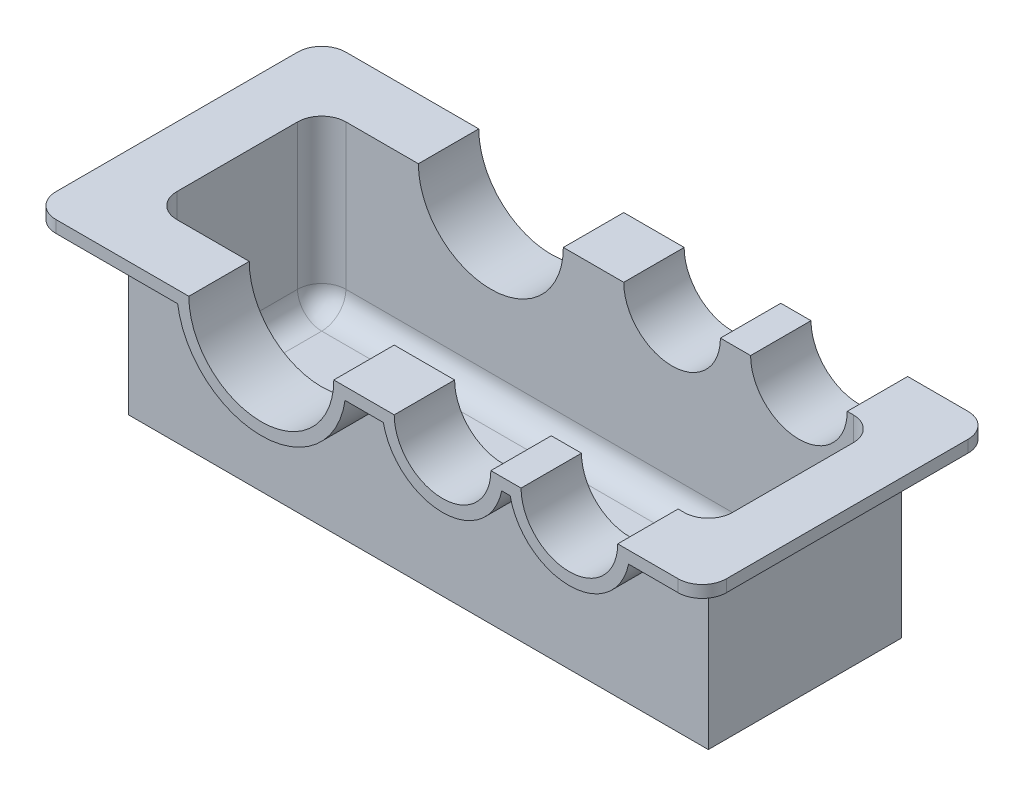
SolidWorks part; units mm, degrees
ref_plane "Front Plane" through (0, 0, 0) normal (0, 0, 1) x (1, 0, 0)
ref_plane "Top Plane" through (0, 0, 0) normal (0, 1, 0) x (1, 0, 0)
ref_plane "Right Plane" through (0, 0, 0) normal (1, 0, 0) x (0, 0, -1)
sketch "Sketch1" plane through (0, 0, 0) normal (1, 0, 0) x (0, 0, -1)
  line L0 (0, 36.5824) -> (0, 125.8036) construction
  line L10 (80, 150) -> (-80, 150)
  line L11 (80, 150) -> (80, 0)
  line L12 (80, 0) -> (-80, 0)
  line L13 (-80, 150) -> (-80, 0)
  line L14 (80, 150) -> (-80, 0) construction
  line L15 (80, 0) -> (-80, 150) construction
  point P0 (0, 75)
  dimension "D1" = 160
  dimension "D2" = 150
extrude "Boss-Extrude1" add sketch "Sketch1" along normal mid plane 480
shell "Shell1" thickness 10
sketch "Sketch2" plane through (0, 0, 0) normal (0, 0, 1) x (1, 0, 0)
  line L0 (240, 150) -> (-240, 150) construction
  circle A0 centre (-90, 150) radius 60
  circle A1 centre (60, 150) radius 40
  circle A2 centre (165, 150) radius 40
  dimension "D2" = 80
  dimension "D4" = 80
  dimension "D6" = 120
  dimension "D1" = 75
  dimension "D3" = 105
  dimension "D5" = 150
extrude "Cut-Extrude1" cut sketch "Sketch2" against normal through all both and the other way through all
sketch "Sketch3" plane through (0, 0, 0) normal (0, 0, 1) x (1, 0, 0)
  line L0 (125, 150) -> (100, 150) construction
  line L1 (20, 150) -> (-30, 150) construction
  line L2 (125, 150) -> (100, 150)
  line L3 (20, 150) -> (-30, 150)
  line L4 (-150, 150) -> (-280, 150)
  line L5 (205, 150) -> (275, 150)
  arc A0 (-150, 150) -> (-30, 150) centre (-90, 150) ccw construction
  arc A1 (-150, 150) -> (-30, 150) centre (-90, 150) ccw
  arc A2 (125, 150) -> (205, 150) centre (165, 150) ccw construction
  arc A3 (20, 150) -> (100, 150) centre (60, 150) ccw construction
  arc A4 (125, 150) -> (205, 150) centre (165, 150) ccw
  arc A5 (20, 150) -> (100, 150) centre (60, 150) ccw
  dimension "D1" = 130
  dimension "D2" = 70
extrude "Extrude-Thin1" add sketch "Sketch3" along normal mid plane 240 thin thin type one direction wall 10
sketch "Sketch4" plane through (0, 150, 0) normal (0, 1, 0) x (1, 0, 0)
  line L0 (230, -70) -> (230, 70) construction
  line L1 (-230, -70) -> (230, -70)
  line L2 (-230, -70) -> (-230, 70)
  line L3 (-230, 70) -> (230, 70)
  line L4 (230, -70) -> (230, 70)
  line L5 (-230, -70) -> (230, 70) construction
  line L6 (-230, 70) -> (230, -70) construction
  point P0 (0, 0)
extrude "Cut-Extrude2" cut sketch "Sketch4" against normal blind 100
fillet "Fillet1" radius 20 4 edges at (275, 145, 120) (275, 145, -120) (-280, 145, -120) (-280, 145, 120)
fillet "Fillet2" radius 20 8 edges at (-230, 10, 0) (0, 10, 70) (-230, 80, -70) (0, 10, -70) (230, 10, 0) (230, 80, -70) (-230, 80, 70) (230, 80, 70)
